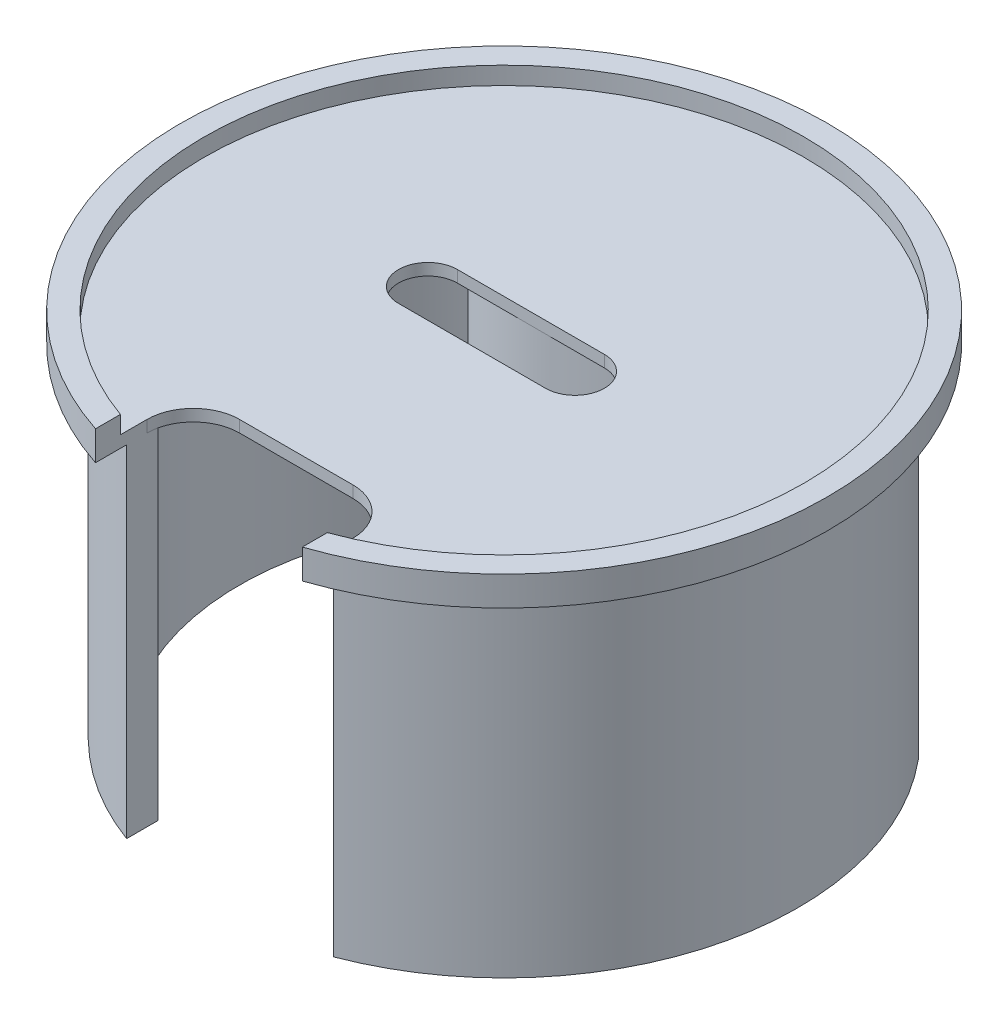
SolidWorks part; units mm, degrees
ref_plane "Front Plane" through (0, 0, 0) normal (0, 0, 1) x (1, 0, 0)
ref_plane "Top Plane" through (0, 0, 0) normal (0, 1, 0) x (1, 0, 0)
ref_plane "Right Plane" through (0, 0, 0) normal (1, 0, 0) x (0, 0, -1)
sketch "Sketch3" plane through (0, 0, 0) normal (0, 1, 0) x (1, 0, 0)
  line L0 (-16.4485, 0) -> (15.3015, 0) construction
  line L1 (-16.4485, 6.35) -> (15.3015, 6.35)
  line L2 (-16.4485, -6.35) -> (15.3015, -6.35)
  circle A0 centre (0, 0) radius 69.85
  arc A2 (-16.4485, 6.35) -> (-16.4485, -6.35) centre (-16.4485, 0) ccw
  arc A3 (15.3015, -6.35) -> (15.3015, 6.35) centre (15.3015, 0) ccw
  point P5 (-0.5735, 0)
extrude "Boss-Extrude1" add sketch "Sketch3" along normal blind 6.35
sketch "Sketch4" plane through (0, 6.35, 0) normal (0, 1, 0) x (1, 0, 0)
  circle A0 centre (0, 0) radius 64.77
extrude "Cut-Extrude1" cut sketch "Sketch4" against normal blind 3.81
sketch "Sketch5" plane through (0, 6.35, 0) normal (0, 1, 0) x (1, 0, 0)
  line L1 (22.5372, -45.2053) -> (-21.9128, -45.2053)
  line L2 (22.5372, -45.2053) -> (22.5372, -70.6053)
  line L3 (22.5372, -70.6053) -> (-21.9128, -70.6053)
  line L4 (-21.9128, -45.2053) -> (-21.9128, -70.6053)
  dimension "D1" = 25.4
  dimension "D2" = 44.45
extrude "Cut-Extrude2" cut sketch "Sketch5" against normal through all
fillet "Fillet1" radius 10 2 edges at (22.5372, 1.27, 45.2053) (-21.9128, 1.27, 45.2053)
sketch "Sketch8" plane through (0, 0, 0) normal (0, -1, 0) x (1, 0, 0)
  line L0 (34.2582, -40.64) -> (30.4482, -40.64)
  line L1 (-30.4482, -40.64) -> (-34.2582, -40.64)
  arc A3 (34.2582, -40.64) -> (-34.2582, -40.64) centre (0, -40.64) ccw
  arc A4 (30.4482, -40.64) -> (-30.4482, -40.64) centre (0, -40.64) ccw
  point P0 (0, -40.64)
  dimension "D2" = 3.81
  dimension "D1" = 40.64
extrude "Boss-Extrude2" add sketch "Sketch8" along normal blind 31.75
sketch "Sketch11" plane through (0, 2.54, 0) normal (0, 1, 0) x (1, 0, 0)
  line L0 (-40.181, 40.64) -> (-48.7918, 40.64)
  line L1 (-48.7918, 40.64) -> (-40.181, 40.64)
  line L2 (40.181, 40.64) -> (48.7918, 40.64)
  line L3 (-21.9128, -59.5993) -> (-21.9128, -52.7821)
  line L4 (-21.9128, -55.2053) -> (-21.9128, -66.3238) construction
  line L5 (22.5372, -59.366) -> (22.5372, -52.5186)
  line L6 (22.5372, -66.1143) -> (22.5372, -55.2053) construction
  arc A1 (-40.181, 40.64) -> (-21.9128, -52.7821) centre (0, 0) ccw
  arc A3 (22.5372, -52.5186) -> (40.181, 40.64) centre (0, 0) ccw
  arc A4 (-48.7918, 40.64) -> (-21.5904, -59.7169) centre (0, 0) ccw
  arc A5 (22.5372, -59.366) -> (48.7918, 40.64) centre (0, 0) ccw
  line M1 (22.5372, -55.2053) -> (22.5372, -60.7226)
  line M3 (-21.9128, -60.9506) -> (-21.9128, -55.2053)
extrude "Boss-Extrude3" add sketch "Sketch11" against normal blind 76.2 contours L0 A4 L3 A1 M3 | A5 L2 A3 L5 M1
